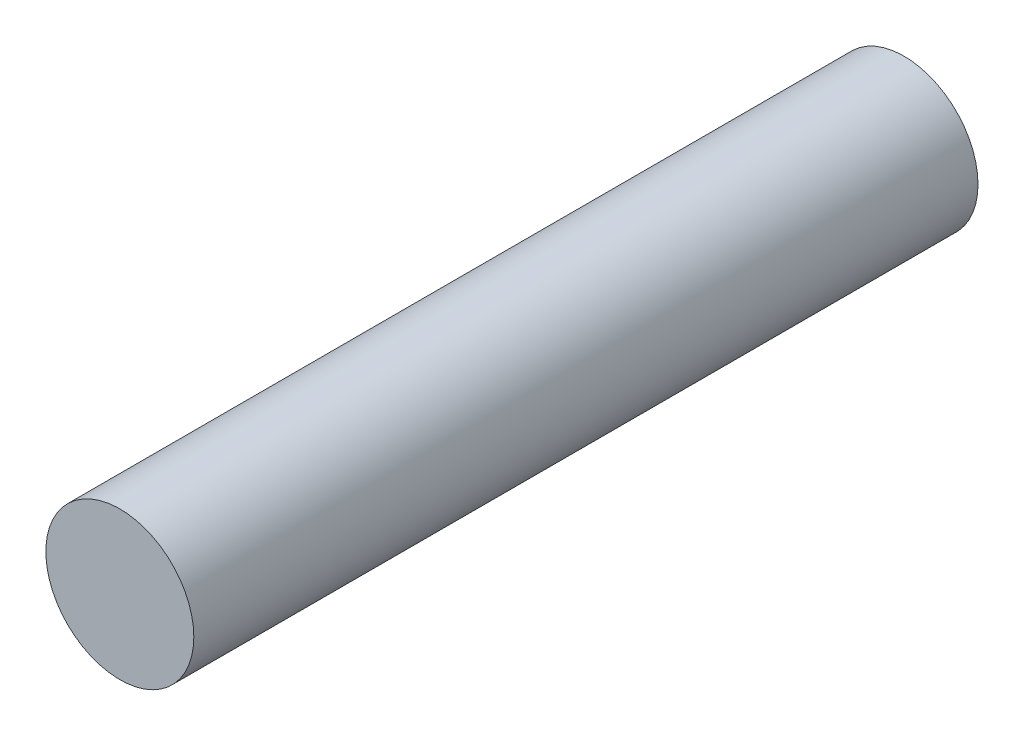
SolidWorks part; units mm, degrees
ref_plane "Front Plane" through (0, 0, 0) normal (0, 0, 1) x (1, 0, 0)
ref_plane "Top Plane" through (0, 0, 0) normal (0, 1, 0) x (1, 0, 0)
ref_plane "Right Plane" through (0, 0, 0) normal (1, 0, 0) x (0, 0, -1)
sketch "Sketch1" plane through (0, 0, 0) normal (0, 0, 1) x (1, 0, 0)
  circle A0 centre (0, 0) radius 2
  dimension "D1" = 4
extrude "Extrude1" add sketch "Sketch1" against normal blind 21.2
